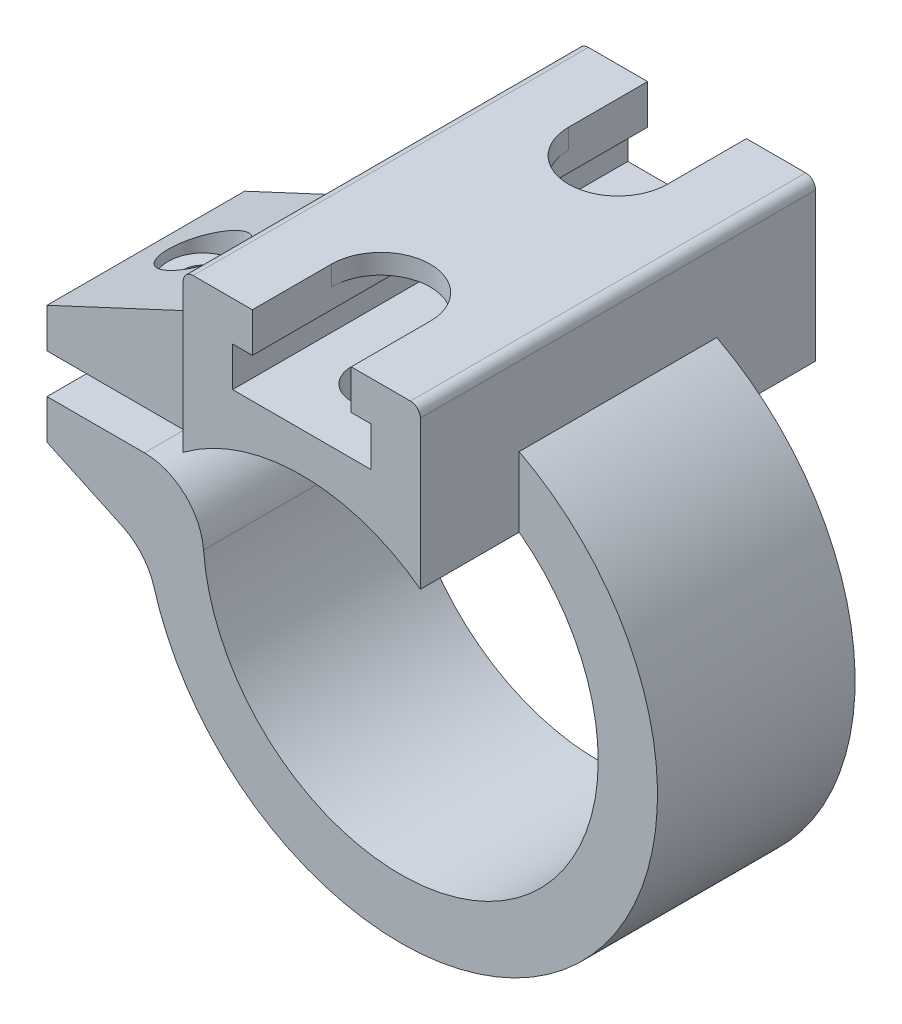
SolidWorks part; units mm, degrees
material "Plain Carbon Steel"
ref_plane "Front Plane" through (0, 0, 0) normal (0, 0, 1) x (1, 0, 0)
ref_plane "Top Plane" through (0, 0, 0) normal (0, 1, 0) x (1, 0, 0)
ref_plane "Right Plane" through (0, 0, 0) normal (1, 0, 0) x (0, 0, -1)
sketch "Sketch1" plane through (0, 0, 0) normal (0, 0, 1) x (1, 0, 0)
  line L0 (-25.3777, 0) -> (25.3777, 0) construction
  line L1 (-17.8936, 0) -> (-12.7794, -2.3848)
  line L2 (-17.8936, 0) -> (-17.8936, 6)
  line L3 (-17.8936, 6) -> (-5.494, 11.782)
  arc A8 (-12.7794, -2.3848) -> (-5.494, 11.782) centre (0, 0) ccw
  point P6 (0, 0)
  point P19 (-17.8936, 0)
  dimension "D1" = 25
  dimension "D2" = 6
  dimension "D7" = 13
  dimension "D4" = 25
extrude "Boss-Extrude1" add sketch "Sketch1" along normal mid plane 10
sketch "Sketch2" plane through (0, 0, 5) normal (0, 0, 1) x (1, 0, 0)
  line L1 (-17.8936, 6) -> (-17.8936, 0) construction
  line L3 (-17.8936, 4) -> (-10.9545, 4)
  line L4 (-17.8936, 4) -> (-17.8936, 2)
  line L5 (-17.8936, 2) -> (-12.9615, 2)
  arc A0 (-9.9704, -0.7692) -> (-8.4265, 5.3846) centre (0, 0) ccw
  arc A4 (-9.9704, -0.7692) -> (-12.9615, 2) centre (-12.9615, -1) ccw
  arc A5 (-8.4265, 5.3846) -> (-10.9545, 4) centre (-10.9545, 7) cw
  point P5 (-14.2119, 11.0463)
  point P8 (-18.6384, 2.8125)
  point P9 (-6.831, 5.3095)
  dimension "D1" = 20
  dimension "D3" = 2
  dimension "D4" = 3
  dimension "D2" = 2
extrude "Cut-Extrude1" cut sketch "Sketch2" against normal through all
sketch "Sketch3" plane through (0, 0, 0) normal (0, 0, 1) x (1, 0, 0)
  line L0 (0, 0) -> (0, 21.3861) construction
  line L1 (-5.5, 16) -> (5.5, 16)
  line L2 (6, 15.5) -> (6, 8)
  line L3 (-6, 15.5) -> (-6, 8)
  arc A0 (-9.9704, -0.7692) -> (-8.4265, 5.3846) centre (0, 0) ccw construction
  arc A1 (6, 8) -> (-6, 8) centre (0, 0) ccw
  arc A2 (5.5, 16) -> (6, 15.5) centre (5.5, 15.5) cw
  arc A3 (-6, 15.5) -> (-5.5, 16) centre (-5.5, 15.5) cw
  point P11 (0, 16)
  point P13 (6, 16)
  point P16 (-6, 16)
  dimension "D3" = 0.5
  dimension "D1" = 12
  dimension "D2" = 16
extrude "Boss-Extrude2" add sketch "Sketch3" along normal mid plane 20
sketch "Sketch4" plane through (0, 0, 10) normal (0, 0, 1) x (1, 0, 0)
  line L0 (-2.5, 15) -> (2.5, 15)
  line L1 (2.5, 15) -> (2.5, 14)
  line L2 (2.5, 14) -> (3.5, 14)
  line L3 (3.5, 14) -> (3.5, 12)
  line L4 (3.5, 12) -> (-3.5, 12)
  line L5 (-3.5, 12) -> (-3.5, 14)
  line L6 (-3.5, 14) -> (-2.5, 14)
  line L7 (-2.5, 14) -> (-2.5, 15)
  line L8 (0, 0) -> (0, 16.9573) construction
  line L9 (5.5, 16) -> (-5.5, 16) construction
  dimension "D1" = 7
  dimension "D2" = 5
  dimension "D3" = 2
  dimension "D4" = 1
  dimension "D5" = 1
extrude "Cut-Extrude2" cut sketch "Sketch4" against normal through all
sketch "Sketch5" plane through (0, 16, 0) normal (0, 1, 0) x (1, 0, 0)
  line L0 (-12.4558, 0) -> (12.4558, 0) construction
  line L1 (0, 8.8352) -> (0, -8.8352) construction
  line L2 (-2.5, 6) -> (-2.5, 10)
  line L3 (-2.5, 10) -> (2.5, 10)
  line L5 (2.5, 10) -> (2.5, 6)
  line L6 (5.5, 10) -> (-5.5, 10) construction
  line L7 (2.5, -10) -> (2.5, -6)
  line L8 (-2.5, -10) -> (2.5, -10)
  line L9 (-2.5, -6) -> (-2.5, -10)
  arc A1 (-2.5, 6) -> (2.5, 6) centre (0, 6) ccw
  arc A2 (-2.5, -6) -> (2.5, -6) centre (0, -6) cw
  point P4 (0, 0)
  point P9 (0, 0)
  dimension "D1" = 2.5
  dimension "D2" = 4
extrude "Cut-Extrude3" cut sketch "Sketch5" against normal up to next
sketch "Sketch6" plane through (0, 12, 0) normal (0, 1, 0) x (1, 0, 0)
  line L0 (0, 0) -> (4.8358, 0) construction
  circle A0 centre (0, 6) radius 1.5
  circle A1 centre (0, -6) radius 1.5
  dimension "D1" = 3
extrude "Cut-Extrude4" cut sketch "Sketch6" against normal up to next
ref_plane "Plane1" through (0, 16, 0) normal (0, 1, 0) x (1, 0, 0)
sketch "Sketch9" plane through (0, 16, 0) normal (0, 1, 0) x (1, 0, 0)
  line L0 (17.3112, 0) -> (-17.3112, 0) construction
  circle A0 centre (-15, 0) radius 1.75
  point P4 (0, 0)
  dimension "D1" = 3.5
  dimension "D2" = 15
extrude "Cut-Extrude7" cut sketch "Sketch9" against normal offset from surface (10 mm away) 2 contours A0 up to face at (-14.424, 4, 0)
sketch "Sketch10" plane through (0, 16, 0) normal (0, 1, 0) x (1, 0, 0)
  circle A0 centre (-15, 0) radius 1
  circle A1 centre (-15, 0) radius 1.75 construction
  dimension "D1" = 2
extrude "Cut-Extrude6" cut sketch "Sketch10" against normal through all
fillet "Fillet9" radius 3 1 edges at (-12.7794, -2.3848, 0)
